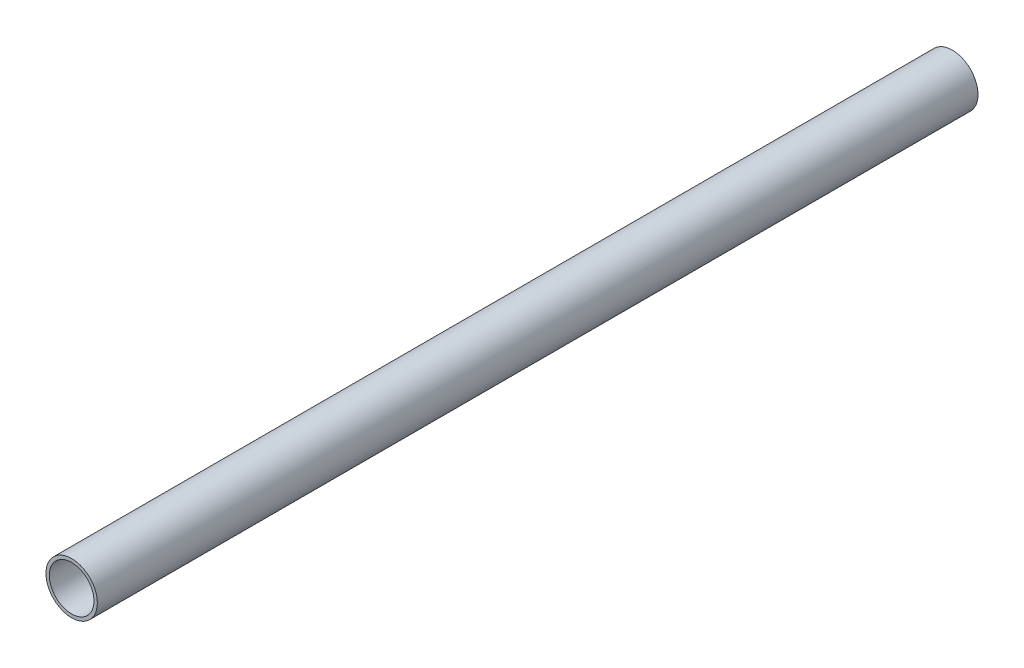
SolidWorks part; units mm, degrees
material "PVC Rigid"
ref_plane "Front Plane" through (0, 0, 0) normal (0, 0, 1) x (1, 0, 0)
ref_plane "Top Plane" through (0, 0, 0) normal (0, 1, 0) x (1, 0, 0)
ref_plane "Right Plane" through (0, 0, 0) normal (1, 0, 0) x (0, 0, -1)
sketch "Sketch1" plane through (0, 0, 0) normal (0, 0, 1) x (1, 0, 0)
  circle A0 centre (0, 0) radius 44.45
  circle A2 centre (0, 0) radius 38.6334
  dimension "D1" = 88.9
  dimension "D2" = 77.2668
extrude "Boss-Extrude1" add sketch "Sketch1" along normal blind 1524
